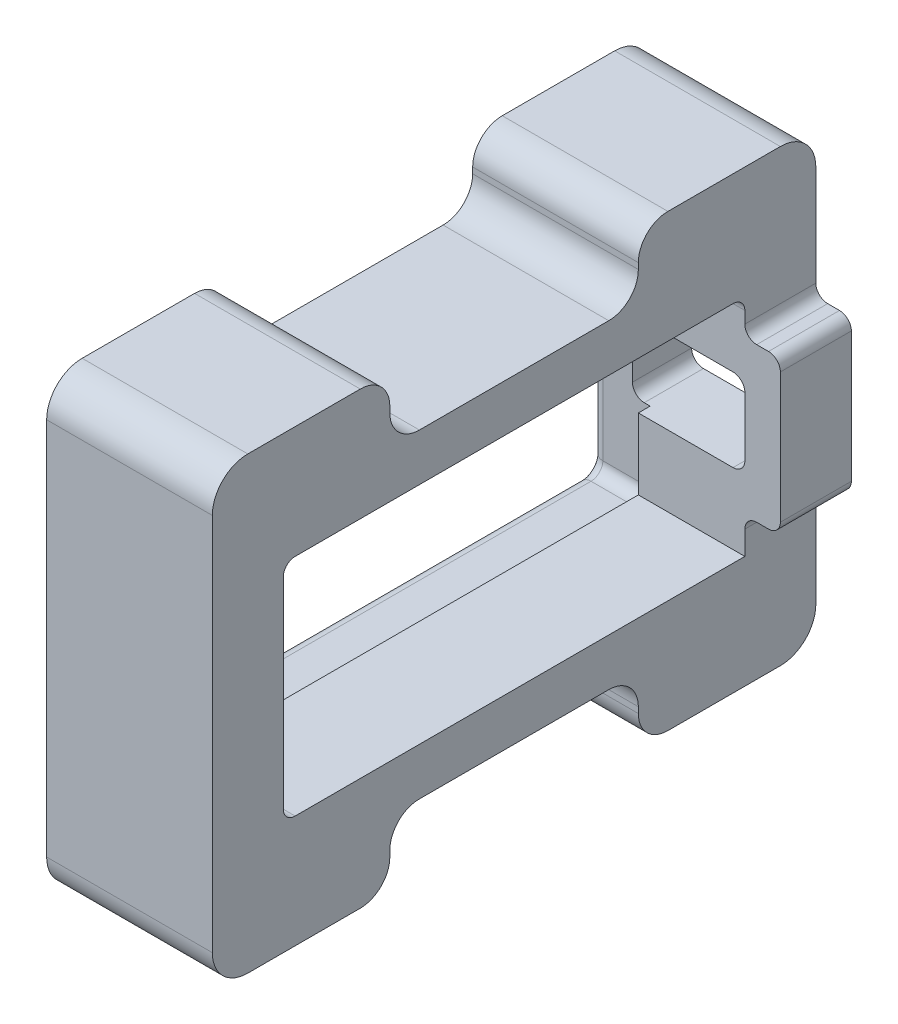
SolidWorks part; units mm, degrees
material "ABS"
ref_plane "Front Plane" through (0, 0, 0) normal (0, 0, 1) x (1, 0, 0)
ref_plane "Top Plane" through (0, 0, 0) normal (0, 1, 0) x (1, 0, 0)
ref_plane "Right Plane" through (0, 0, 0) normal (1, 0, 0) x (0, 0, -1)
sketch "Sketch1" plane through (0, 0, 0) normal (1, 0, 0) x (0, 0, -1)
  line L0 (-25.5, -19) -> (25.5, -19)
  line L1 (-25.5, -19) -> (-25.5, 19)
  line L2 (25.5, -19) -> (25.5, 19)
  line L3 (-25.5, 19) -> (25.5, 19)
  line L4 (-25.5, -19) -> (25.5, 19) construction
  line L5 (25.5, -19) -> (-25.5, 19) construction
  line L6 (-20.5, -10.5) -> (20.5, -10.5)
  line L7 (-20.5, -10.5) -> (-20.5, 10.5)
  line L8 (20.5, -10.5) -> (20.5, 10.5)
  line L9 (-20.5, 10.5) -> (20.5, 10.5)
  line L10 (-20.5, -10.5) -> (20.5, 10.5) construction
  line L11 (20.5, -10.5) -> (-20.5, 10.5) construction
  point P1 (0, 0)
  point P2 (0, 0)
  dimension "D1" = 38
  dimension "D2" = 51
  dimension "D3" = 41
  dimension "D4" = 21
extrude "Main Body" add sketch "Sketch1" along normal mid plane 20
sketch "Sketch2" plane through (0, 0, 0) normal (1, 0, 0) x (0, 0, -1)
  line L1 (-19.5, 9.5) -> (-19.5, -9.5)
  line L2 (-19.5, -9.5) -> (19.5, -9.5)
  line L3 (19.5, -9.5) -> (19.5, 9.5)
  line L4 (19.5, 9.5) -> (-19.5, 9.5)
  line L5 (-20.5, 10.5) -> (-20.5, -10.5)
  line L6 (20.5, 10.5) -> (-20.5, 10.5)
  line L7 (20.5, -10.5) -> (20.5, 10.5)
  line L8 (-20.5, -10.5) -> (20.5, -10.5)
  line L9 (-20.5, 10.5) -> (-20.5, -10.5)
  line L10 (20.5, 10.5) -> (-20.5, 10.5)
  line L11 (20.5, -10.5) -> (20.5, 10.5)
  line L12 (-20.5, -10.5) -> (20.5, -10.5)
  dimension "D1" = 0
  dimension "D2" = 1
extrude "End Stop" add sketch "Sketch2" along normal mid plane 10
fillet "Contouring" radius 1 11 edges at (7.5, 10.5, -20.5) (0, 9.5, -19.5) (-7.5, 10.5, -20.5) (-7.5, 10.5, 20.5) (0, 9.5, 19.5) (7.5, 10.5, 20.5) (0, -9.5, 19.5) (7.5, -10.5, 20.5) (7.5, -10.5, -20.5) (-7.5, -10.5, -20.5) (-7.5, -10.5, 20.5)
sketch "Sketch4" plane through (10, 0, 0) normal (1, 0, 0) x (0, 0, -1)
  line L0 (0, 19) -> (0, -19) construction
  line L1 (25.5, 19) -> (-25.5, 19) construction
  line L2 (-25.5, -19) -> (25.5, -19) construction
  line L3 (19.5, 10.5) -> (-19.5, 10.5) construction
  line L4 (-10.5, 19) -> (10.5, 19)
  line L5 (-10.5, 19) -> (-10.5, 13.5)
  line L6 (-10.5, 13.5) -> (10.5, 13.5)
  line L7 (10.5, 19) -> (10.5, 13.5)
  line L8 (0, 0) -> (-25.5, 0) construction
  line L9 (-25.5, 19) -> (-25.5, -19) construction
  line L10 (-10.5, -19) -> (-10.5, -13.5)
  line L11 (-10.5, -13.5) -> (10.5, -13.5)
  line L12 (10.5, -19) -> (10.5, -13.5)
  line L13 (-10.5, -19) -> (10.5, -19)
  dimension "D1" = 3
  dimension "D2" = 15
extrude "Clearance - Middle" cut sketch "Sketch4" against normal through all
fillet "Edge Contouring" radius 3 4 edges at (0, 19, -25.5) (0, -19, -25.5) (0, -19, 25.5) (0, 19, 25.5)
fillet "Inner Contouring" radius 2.5 8 edges at (0, -19, -10.5) (0, -13.5, -10.5) (0, -19, 10.5) (0, -13.5, 10.5) (0, 19, -10.5) (0, 13.5, -10.5) (0, 13.5, 10.5) (0, 19, 10.5)
fillet "Fit Contouring" radius 1 16 edges at (10, 10.2071, -20.2071) (10, 0, -20.5) (10, -10.2071, -20.2071) (10, -10.5, 0) (10, -10.2071, 20.2071) (10, 0, 20.5) (10, 10.2071, 20.2071) (-10, 10.2071, -20.2071) (-10, 0, -20.5) (-10, -10.2071, -20.2071) (-10, -10.5, 0) (-10, -10.2071, 20.2071) (-10, 0, 20.5) (-10, 10.2071, 20.2071) (10, 10.5, 0) (-10, 10.5, 0)
sketch "Sketch5" plane through (0, 0, -25.5) normal (0, 0, -1) x (-1, 0, 0)
  line L0 (0, 0) -> (-32.5677, 0) construction
  line L1 (-4, 27.1392) -> (-19.3585, 27.1392)
  line L2 (-4, 27.1392) -> (-4, -27.1392)
  line L3 (-4, -27.1392) -> (-19.3585, -27.1392)
  line L4 (-19.3585, 27.1392) -> (-19.3585, -27.1392)
  dimension "D1" = 4
extrude "Single Cut" cut sketch "Sketch5" against normal through all
sketch "Sketch6" plane through (0, 0, -25.5) normal (0, 0, -1) x (-1, 0, 0)
  line L1 (-6.5, -3.5) -> (6.5, -3.5)
  line L2 (-6.5, -3.5) -> (-6.5, 3.5)
  line L3 (-6.5, 3.5) -> (6.5, 3.5)
  line L4 (6.5, -3.5) -> (6.5, 3.5)
  line L5 (-6.5, -3.5) -> (6.5, 3.5) construction
  line L6 (-6.5, 3.5) -> (6.5, -3.5) construction
  point P0 (0, 0)
  dimension "D1" = 7
  dimension "D2" = 13
extrude "Clearance - Wire" cut sketch "Sketch6" against normal up to surface (6 mm away) up to face at (-0.5, -0.5, -19.5)
sketch "Sketch7" plane through (0, 0, -25.5) normal (0, 0, -1) x (-1, 0, 0)
  line L0 (-4, 3.5) -> (-4, 16) construction
  line L1 (-4, 6.5) -> (-7, 6.5)
  line L2 (-4, 6.5) -> (-4, -6.5)
  line L3 (-4, -6.5) -> (-7, -6.5)
  line L4 (-7, 6.5) -> (-7, -6.5)
  line L5 (0, 0) -> (-4, 0) construction
  line L6 (6.5, 3.5) -> (-4, 3.5) construction
  dimension "D1" = 3
  dimension "D2" = 3
extrude "Wire Cap" add sketch "Sketch7" against normal up to surface (6 mm away) up to face at (-0.5, 6, -19.5)
fillet "Wire Clearance Contouring" radius 1 8 edges at (4, -6.5, -22.5) (7, -6.5, -22.5) (7, 6.5, -22.5) (4, 6.5, -22.5) (4, 3.5, -22.5) (4, -3.5, -22.5) (-6.5, -3.5, -23) (-6.5, 3.5, -23)
ref_point "Point1"
equation "\"D1@Sketch7\"=\"width keep@values@params_print.sldprt\""
equation "\"D2@Sketch7\"=\"width keep@values@params_print.sldprt\""
